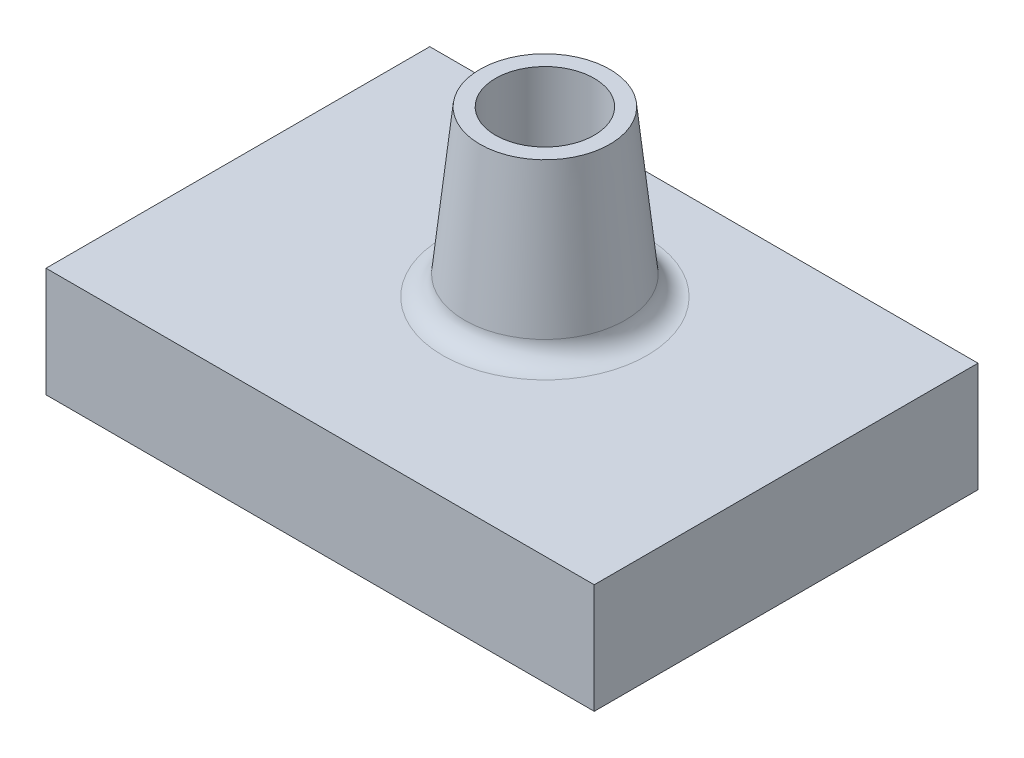
SolidWorks part; units mm, degrees
ref_plane "Front Plane" through (0, 0, 0) normal (0, 0, 1) x (1, 0, 0)
ref_plane "Top Plane" through (0, 0, 0) normal (0, 1, 0) x (1, 0, 0)
ref_plane "Right Plane" through (0, 0, 0) normal (1, 0, 0) x (0, 0, -1)
sketch "Sketch1" plane through (0, 0, 0) normal (0, 1, 0) x (1, 0, 0)
  line L1 (-25, 17.5) -> (25, 17.5)
  line L2 (-25, 17.5) -> (-25, -17.5)
  line L3 (-25, -17.5) -> (25, -17.5)
  line L4 (25, 17.5) -> (25, -17.5)
  line L5 (-25, 17.5) -> (25, -17.5) construction
  line L6 (-25, -17.5) -> (25, 17.5) construction
  point P0 (0, 0)
  dimension "D1" = 35
  dimension "D2" = 50
extrude "Boss-Extrude1" add sketch "Sketch1" along normal blind 10
sketch "Sketch2" plane through (0, 10, 0) normal (0, 1, 0) x (1, 0, 0)
  circle A0 centre (0, 3) radius 7.5
  dimension "D1" = 15
extrude "Boss-Extrude2" add sketch "Sketch2" along normal blind 15 draft 6
sketch "Sketch3" plane through (0, 25, 0) normal (0, 1, 0) x (1, 0, 0)
  circle A0 centre (0, 3) radius 4.5
  dimension "D1" = 9
extrude "Cut-Extrude1" cut sketch "Sketch3" against normal blind 15
fillet "Fillet1" radius 2 1 edges at (0, 10, 4.5)
